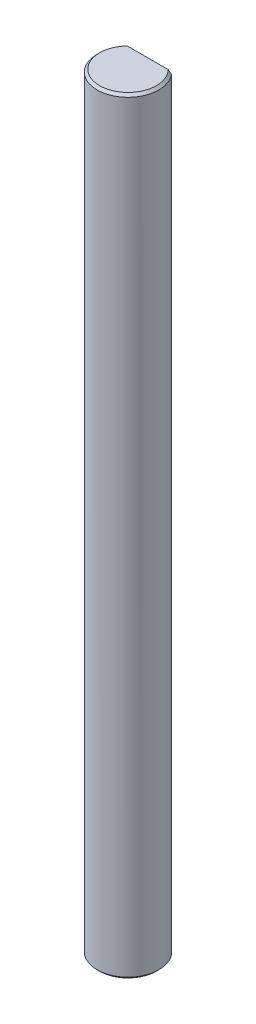
SolidWorks part; units mm, degrees
ref_plane "Alzado" through (0, 0, 0) normal (0, 0, 1) x (1, 0, 0)
ref_plane "Planta" through (0, 0, 0) normal (0, 1, 0) x (1, 0, 0)
ref_plane "Vista lateral" through (0, 0, 0) normal (1, 0, 0) x (0, 0, -1)
sketch "Croquis1" plane through (0, 0, 0) normal (0, 1, 0) x (1, 0, 0)
  circle A0 centre (0, 0) radius 2.5
  dimension "D1" = 5
extrude "Saliente-Extruir1" add sketch "Croquis1" along normal offset from surface (62 mm away) 20 contours A0
sketch "Croquis2" plane through (0, 62, 0) normal (0, 1, 0) x (1, 0, 0)
  line L0 (-1.9209, 1.6) -> (1.9209, 1.6)
  line L1 (0, -2.5) -> (0, 1.6) construction
  circle A0 centre (0, 0) radius 2.5 construction
  arc A1 (1.9209, 1.6) -> (-1.9209, 1.6) centre (0, 0) ccw
  dimension "D1" = 4.1
extrude "Cortar-Extruir1" cut sketch "Croquis2" against normal blind 17.5
chamfer "Chaflán1" distance 0.2 angle 45 2 edges at (0, 0, 2.5) (0, 62, 2.5)
